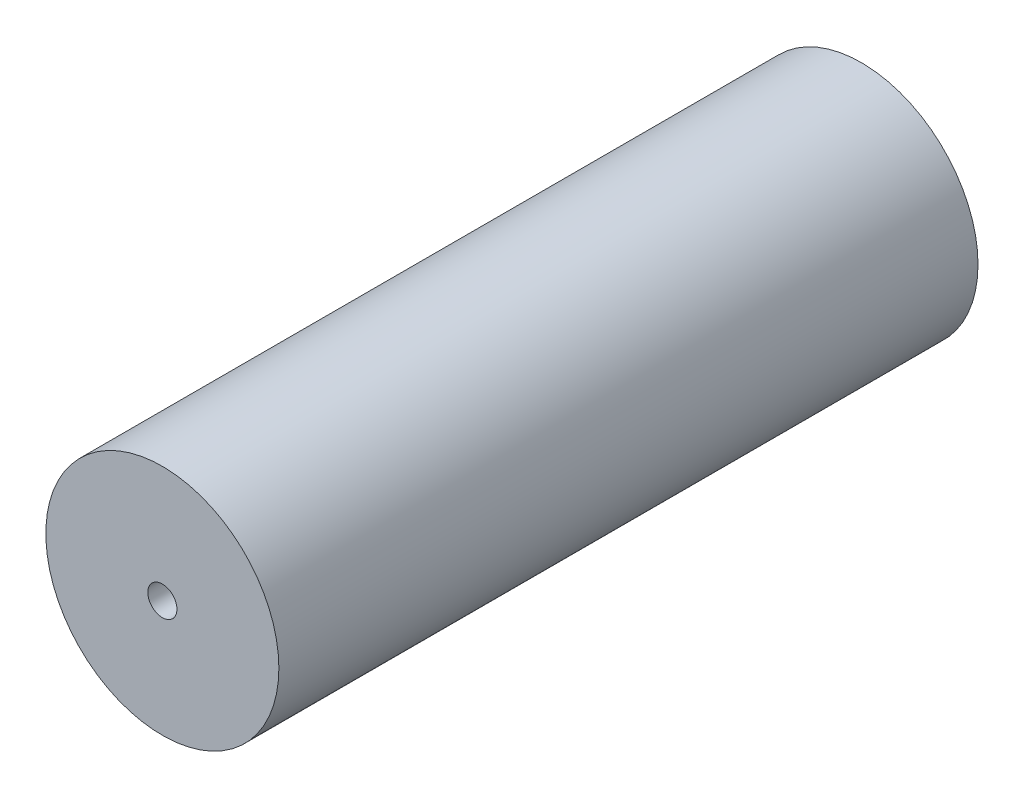
SolidWorks part; units mm, degrees
ref_plane "Front Plane" through (0, 0, 0) normal (0, 0, 1) x (1, 0, 0)
ref_plane "Top Plane" through (0, 0, 0) normal (0, 1, 0) x (1, 0, 0)
ref_plane "Right Plane" through (0, 0, 0) normal (1, 0, 0) x (0, 0, -1)
sketch "Sketch1" plane through (0, 0, 0) normal (0, 0, 1) x (1, 0, 0)
  line L1 (-25.4, 0) -> (25.4, 0) construction
  dimension "OD" = 50.8
sketch "Sketch2" plane through (0, 0, 0) normal (1, 0, 0) x (0, 0, -1)
  line L0 (152.4, 0) -> (-152.4, 0)
  point P4 (0, 0)
  dimension "Length" = 304.8
sketch "Sketch3" plane through (0, 0, 0) normal (0, 0, 1) x (1, 0, 0)
  circle A0 centre (0, 0) radius 25.4
extrude "Boss-Extrude1" add sketch "Sketch3" along normal blind 152.4
sketch "Sketch4" plane through (0, 0, 152.4) normal (0, 0, 1) x (1, 0, 0)
  circle A0 centre (0, 0) radius 3.175
  dimension "D1" = 6.35
extrude "Cut-Extrude1" cut sketch "Sketch4" against normal blind 25.4
